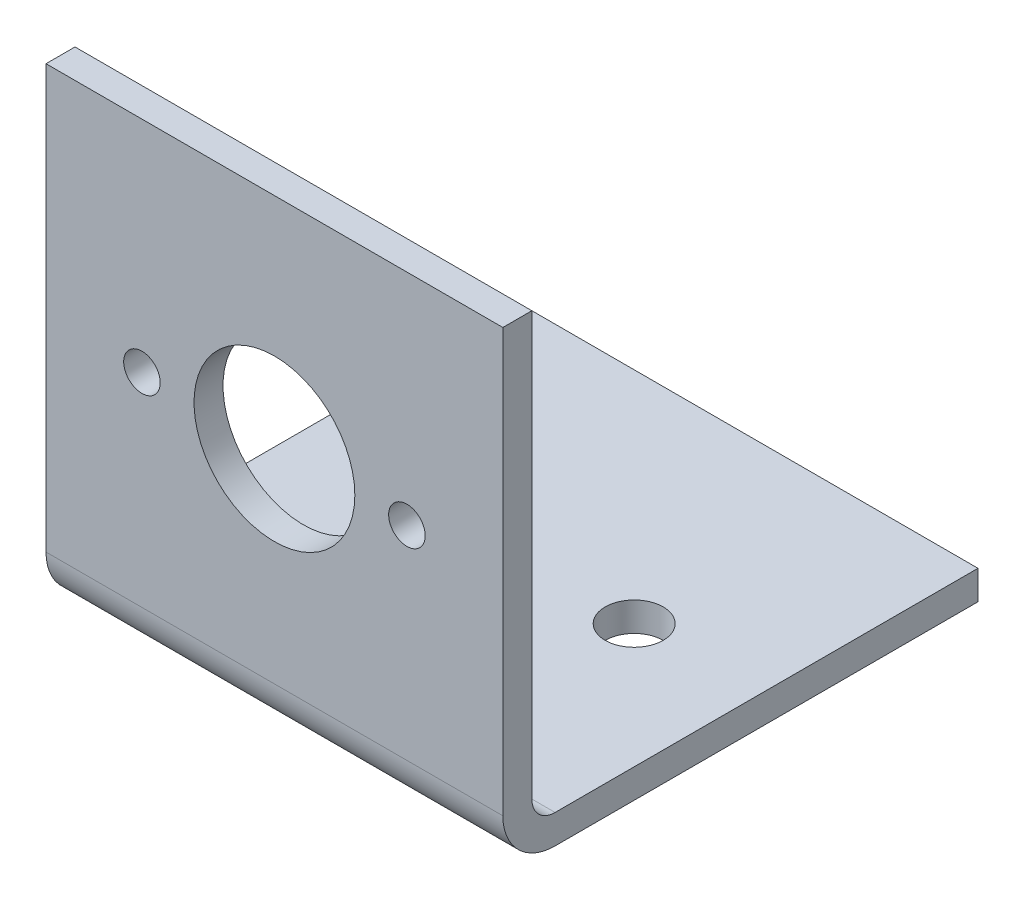
SolidWorks part; units mm, degrees
ref_plane "Front Plane" through (0, 0, 0) normal (0, 0, 1) x (1, 0, 0)
ref_plane "Top Plane" through (0, 0, 0) normal (0, 1, 0) x (1, 0, 0)
ref_plane "Right Plane" through (0, 0, 0) normal (1, 0, 0) x (0, 0, -1)
sketch "Sketch1" plane through (0, 0, 0) normal (1, 0, 0) x (0, 0, -1)
  line L0 (0, 0) -> (0, -52)
  line L1 (0, -52) -> (52, -52)
  line L2 (52, -52) -> (52, -48.825)
  line L3 (52, -48.825) -> (3.175, -48.825)
  line L4 (3.175, -48.825) -> (3.175, 0)
  line L5 (3.175, 0) -> (0, 0)
  dimension "D1" = 3.175
  dimension "D2" = 52
extrude "Boss-Extrude1" add sketch "Sketch1" along normal blind 50
fillet "Fillet1" radius 2.54 1 edges at (25, -48.825, -3.175)
fillet "Fillet2" radius 5.715 1 edges at (25, -52, 0)
sketch "Sketch2" plane through (0, 0, 0) normal (0, 0, 1) x (1, 0, 0)
  line L0 (50, -52) -> (0, -52) construction
  line L1 (10.5, -24) -> (39.5, -24) construction
  line L2 (0, 0) -> (0, -46.285) construction
  circle A0 centre (25, -24) radius 8.8
  circle A1 centre (10.5, -24) radius 2
  circle A2 centre (39.5, -24) radius 2
  dimension "D4" = 17.6
  dimension "D5" = 4
  dimension "D1" = 28
  dimension "D2" = 25
  dimension "D3" = 29
  dimension "D6" = 14.5
extrude "Cut-Extrude1" cut sketch "Sketch2" against normal through all both and the other way through all
sketch "Sketch3" plane through (0, -52, 0) normal (0, -1, 0) x (1, 0, 0)
  line L0 (-6.5594, -26) -> (58.4997, -26) construction
  line L2 (50, -52) -> (0, -52) construction
  line L3 (-7.6668, -12) -> (57.736, -12) construction
  line L4 (-10.0199, -40) -> (57.736, -40) construction
  line L5 (25, -54.9032) -> (25, -6.5259) construction
  line L6 (0, -5.715) -> (0, -52) construction
  line L7 (36.5, -56.7507) -> (36.5, -7.0314) construction
  line L8 (13.5, -54.3669) -> (13.5, -7.5763) construction
  line L10 (8.5, -38.684) -> (18.5, -38.684)
  line L11 (8.5, -38.684) -> (8.5, -41.316)
  line L12 (8.5, -41.316) -> (18.5, -41.316)
  line L13 (18.5, -38.684) -> (18.5, -41.316)
  point P16 (13.5, -30.9716)
  point P21 (13.5, -38.684)
  point P22 (18.5, -40)
  dimension "D1" = 26
  dimension "D2" = 14
  dimension "D3" = 14
  dimension "D4" = 25
  dimension "D5" = 11.5
  dimension "D6" = 11.5
  dimension "D7" = 10
sketch "Sketch4" plane through (0, -52, 0) normal (0, -1, 0) x (1, 0, 0)
  line L0 (13.57, -27.94) -> (36.43, -27.94) construction
  line L2 (25, -27.94) -> (25, -52) construction
  line L3 (50, -52) -> (0, -52) construction
  line L4 (25, -27.94) -> (25, -12.7) construction
  line L5 (25, -54.9032) -> (25, -6.5259) construction
  line L6 (0, 0) -> (50, 0) construction
  circle A0 centre (13.57, -27.94) radius 3.175
  circle A1 centre (36.43, -27.94) radius 3.175
  circle A2 centre (25, -12.7) radius 3.175
  dimension "D1" = 6.35
  dimension "D2" = 22.86
  dimension "D3" = 15.24
  dimension "D4" = 12.7
extrude "Cut-Extrude2" cut sketch "Sketch4" against normal through all both and the other way through all
